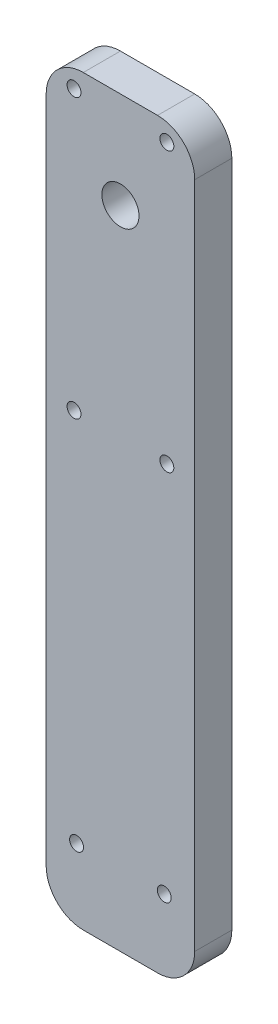
SolidWorks part; units mm, degrees
ref_plane "Front Plane" through (0, 0, 0) normal (0, 0, 1) x (1, 0, 0)
ref_plane "Top Plane" through (0, 0, 0) normal (0, 1, 0) x (1, 0, 0)
ref_plane "Right Plane" through (0, 0, 0) normal (1, 0, 0) x (0, 0, -1)
sketch "Sketch1" plane through (0, 0, 0) normal (0, 0, 1) x (1, 0, 0)
  line L1 (0, 0) -> (25.4, 0)
  line L2 (0, 0) -> (0, 127)
  line L3 (0, 127) -> (25.4, 127)
  line L4 (25.4, 0) -> (25.4, 127)
  dimension "D1" = 127
  dimension "D2" = 25.4
extrude "Boss-Extrude1" add sketch "Sketch1" along normal blind 6.35
sketch "Sketch2" plane through (0, 0, 6.35) normal (0, 0, 1) x (1, 0, 0)
  line L0 (0, 0) -> (25.4, 0) construction
  line L1 (0, 0) -> (25.4, 0) construction
  line L2 (5.2, 4.7625) -> (20.2, 4.7625) construction
  line L3 (5.2, 12.2625) -> (20.2, 12.2625) construction
  circle A3 centre (5.2, 12.2625) radius 1.1906
  circle A4 centre (20.2, 12.2625) radius 1.1906
  point P4 (12.7, 4.7625)
  point P5 (12.7, 0)
  point P8 (12.7, 12.2625)
  dimension "D3" = 7.5
  dimension "D4" = 2.3813
  dimension "D1" = 4.7625
  dimension "D2" = 15
extrude "Cut-Extrude1" cut sketch "Sketch2" against normal up to surface (6.35 mm away) up to face at (12.7, 63.5, 0)
fillet "Fillet1" radius 6.35 4 edges at (0, 0, 3.175) (25.4, 0, 3.175) (0, 127, 3.175) (25.4, 127, 3.175)
sketch "Sketch3" plane through (0, 0, 6.35) normal (0, 0, 1) x (1, 0, 0)
  line L0 (19.05, 127) -> (6.35, 127) construction
  line L1 (19.05, 127) -> (6.35, 127) construction
  circle A0 centre (12.7, 110.4999) radius 3.175
  point P4 (12.7, 127)
  dimension "D2" = 6.35
  dimension "D1" = 16.5001
extrude "Cut-Extrude2" cut sketch "Sketch3" against normal up to surface (6.35 mm away) up to face at (4.0094, 12.2625, 0)
sketch "Sketch4" plane through (0, 0, 6.35) normal (0, 0, 1) x (1, 0, 0)
  line L0 (19.05, 127) -> (6.35, 127) construction
  line L1 (19.05, 127) -> (6.35, 127) construction
  line L2 (4.7625, 123.8123) -> (20.6375, 123.8123) construction
  line L3 (4.7625, 76.1873) -> (20.6375, 76.1873) construction
  circle A0 centre (4.7625, 123.8123) radius 1.1906
  circle A1 centre (20.6375, 123.8123) radius 1.1906
  circle A2 centre (20.6375, 76.1873) radius 1.1906
  circle A3 centre (4.7625, 76.1873) radius 1.1906
  point P6 (12.7, 127)
  point P7 (12.7, 123.8123)
  point P8 (12.7, 76.1873)
  dimension "D4" = 2.3813
  dimension "D1" = 3.1877
  dimension "D2" = 15.875
  dimension "D3" = 50.8127
extrude "Cut-Extrude3" cut sketch "Sketch4" against normal up to surface (6.35 mm away) up to face at (9.525, 110.4999, 0)
